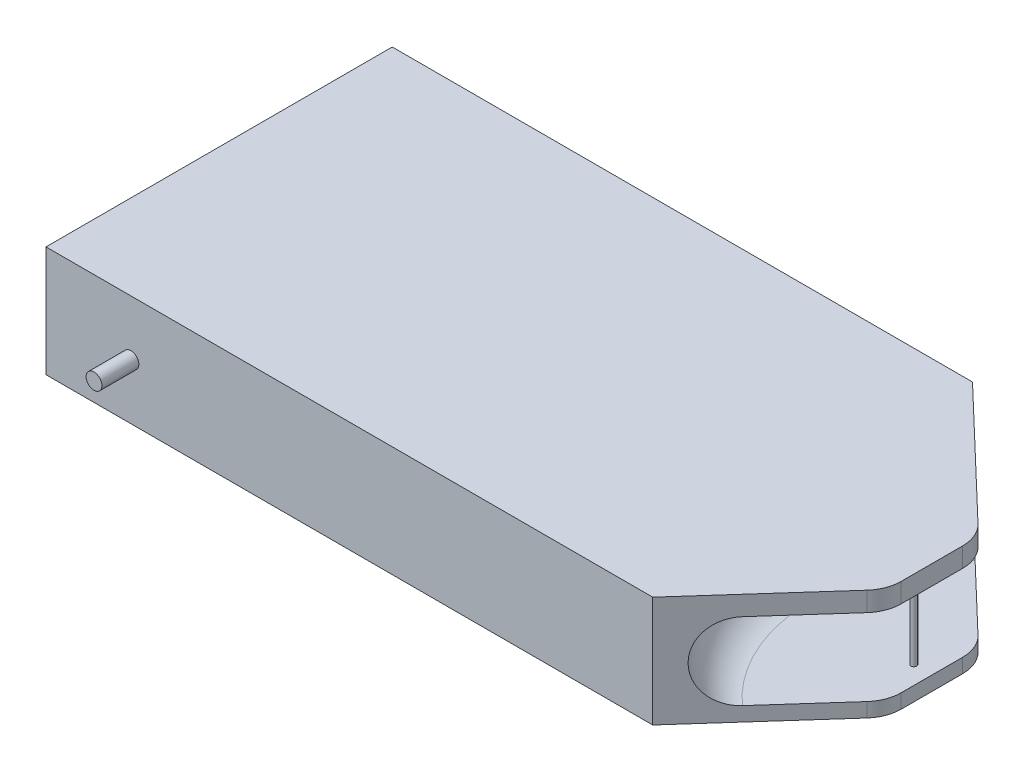
SolidWorks part; units mm, degrees
ref_plane "Front Plane" through (0, 0, 0) normal (0, 0, 1) x (1, 0, 0)
ref_plane "Top Plane" through (0, 0, 0) normal (0, 1, 0) x (1, 0, 0)
ref_plane "Right Plane" through (0, 0, 0) normal (1, 0, 0) x (0, 0, -1)
sketch "Sketch1" plane through (0, 0, 0) normal (0, 1, 0) x (1, 0, 0)
  line L0 (-80.3308, 39.4481) -> (-80.3308, -54.3667)
  line L1 (-80.3308, -54.3667) -> (84.0604, -54.3667)
  line L2 (84.0604, -54.3667) -> (125.9472, -7.4593)
  line L3 (125.9472, -7.4593) -> (76.888, 39.4481)
  line L4 (76.888, 39.4481) -> (-80.3308, 39.4481)
extrude "Boss-Extrude1" add sketch "Sketch1" along normal blind 30
sketch "Sketch2" plane through (73.7782, 0, 65.8814) normal (0.7459, 0, 0.6661) x (0.6661, 0, -0.7459)
  line L0 (32.6472, 14.2957) -> (66.6057, 14.2957) construction
  line L1 (32.6472, 24.7252) -> (66.6057, 24.7252)
  line L2 (32.6472, 3.8662) -> (66.6057, 3.8662)
  arc A1 (32.6472, 24.7252) -> (32.6472, 3.8662) centre (32.6472, 14.2957) ccw
  arc A2 (66.6057, 3.8662) -> (66.6057, 24.7252) centre (66.6057, 14.2957) ccw
  point P2 (49.6264, 14.2957)
revolve "Cut-Revolve2" cut sketch "Sketch2" angle 360 about axis through (125.9472, 30, 7.4593) along (0, -1, 0)
sketch "Sketch3" plane through (0, 0, 54.3667) normal (0, 0, 1) x (1, 0, 0)
  circle A0 centre (-57.3213, 15) radius 2.1462
extrude "Boss-Extrude2" add sketch "Sketch3" along normal blind 10 and the other way blind 104
sketch "Sketch4" plane through (0, 30, 0) normal (0, 1, 0) x (1, 0, 0)
  line L0 (114.0169, 3.9478) -> (114.0169, -20.8196)
  line L1 (125.9472, -7.4593) -> (76.888, 39.4481) construction
  line L2 (84.0604, -54.3667) -> (125.9472, -7.4593) construction
  line L3 (114.0169, -20.8196) -> (176.4895, -20.8196)
  line L4 (176.4895, -20.8196) -> (176.4895, 3.9478)
  line L5 (176.4895, 3.9478) -> (114.0169, 3.9478)
extrude "Cut-Extrude1" cut sketch "Sketch4" against normal through all
fillet "Fillet1" radius 10 4 edges at (114.0169, 1.9331, 20.8196) (114.0169, 1.9331, -3.9478) (114.0169, 27.3626, -3.9478) (114.0169, 27.3626, 20.8196)
sketch "Sketch5" plane through (0, 30, 0) normal (0, 1, 0) x (1, 0, 0)
  circle A0 centre (109.0992, -8.6654) radius 0.7629
extrude "Boss-Extrude3" add sketch "Sketch5" against normal blind 30
sketch "Sketch6" plane through (0, 30, 0) normal (0, 1, 0) x (1, 0, 0)
  line L0 (76.888, 39.4481) -> (-80.3308, 39.4481) construction
  line L1 (-80.3308, -54.3667) -> (84.0604, -54.3667) construction
  line L2 (114.0169, -0.3263) -> (114.0169, -17.0046) construction
  point P0 (98.0169, -8.6654)
  point P1 (36.2169, 19.4481)
  point P2 (36.2169, -34.3667)
  point P10 (114.0169, -8.6654)
  dimension "D1" = 20
  dimension "D2" = 20
  dimension "D3" = 16
sketch "Sketch7" plane through (0, 0, 0) normal (0, -1, 0) x (1, 0, 0)
  point P0 (98.0169, 8.6654)
  point P1 (36.2169, 34.3667)
  point P3 (36.2169, -19.4481)
sketch "Sketch8" plane through (-80.3308, 0, 0) normal (-1, 0, 0) x (0, 0, 1)
  line L1 (-36.7073, 27.9511) -> (51.6259, 27.9511)
  line L2 (-36.7073, 27.9511) -> (-36.7073, 2.0489)
  line L3 (-36.7073, 2.0489) -> (51.6259, 2.0489)
  line L4 (51.6259, 27.9511) -> (51.6259, 2.0489)
  line L5 (-36.7073, 27.9511) -> (51.6259, 2.0489) construction
  line L6 (-36.7073, 2.0489) -> (51.6259, 27.9511) construction
  point P0 (7.4593, 15)
extrude "Cut-Extrude2" cut sketch "Sketch8" against normal blind 5
sketch "Sketch9" plane through (0, 0, 51.6259) normal (0, 0, -1) x (-1, 0, 0)
  circle A0 centre (79.9095, 27.1764) radius 0.25
  point P2 (79.9095, 27.1764)
  dimension "D1" = 0.5
extrude "Boss-Extrude4" add sketch "Sketch9" along normal blind 90 contours A0
